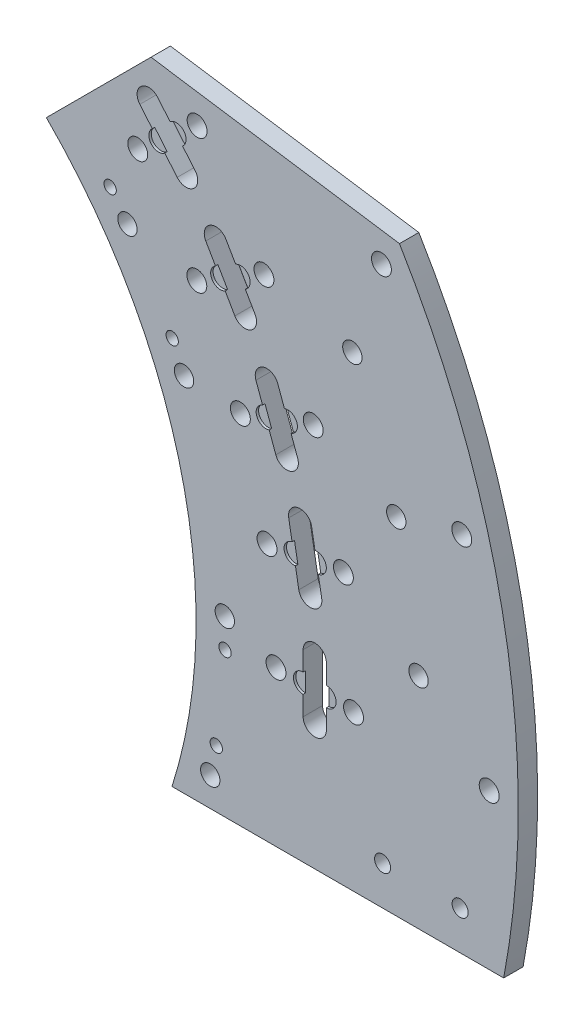
SolidWorks part; units mm, degrees
material "6061-T6 (SS)"
ref_plane "Front Plane" through (0, 0, 0) normal (0, 0, 1) x (1, 0, 0)
ref_plane "Top Plane" through (0, 0, 0) normal (0, 1, 0) x (1, 0, 0)
ref_plane "Right Plane" through (0, 0, 0) normal (1, 0, 0) x (0, 0, -1)
sketch "Sketch1" plane through (0, 0, 0) normal (0, 0, 1) x (1, 0, 0)
  line L0 (0, 0) -> (177.8, 0) construction
  line L1 (176.8984, 6.1774) -> (0, 0) construction
  line L2 (0, 0) -> (121.7947, 121.7947) construction
  line L3 (121.7947, 121.7947) -> (122.9173, 122.9173) construction
  line L4 (144.995, 101.5266) -> (0, 0) construction
  line L5 (0, 0) -> (163.5325, 67.7374) construction
  line L6 (167.4812, 0) -> (167.4812, -50.8) construction
  line L8 (159.5911, -50.8) -> (167.4812, -50.8) construction
  line L9 (172.1267, -41.275) -> (0, 0) construction
  line L10 (159.5911, -50.8) -> (268.2828, -50.8)
  line L11 (118.4271, 118.4271) -> (152.7152, 152.7152)
  line L12 (177.8, 0) -> (193.675, 0) construction
  line L13 (202.565, 0) -> (210.185, 0) construction
  line L14 (210.185, 0) -> (219.075, 0) construction
  line L15 (193.675, 0) -> (202.565, 0) construction
  line L16 (202.565, 0) -> (202.565, 9.525)
  line L17 (202.565, 0) -> (202.565, -9.525)
  line L18 (210.185, 9.525) -> (210.185, 0)
  line L19 (210.185, 0) -> (210.185, -9.525)
  line L20 (202.565, -9.525) -> (210.185, -9.525) construction
  line L21 (202.565, 9.525) -> (210.185, 9.525) construction
  line L22 (210.185, 9.525) -> (219.075, 0) construction
  line L23 (202.565, 9.525) -> (193.675, 0) construction
  line L24 (199.4876, 35.175) -> (201.1416, 25.7947)
  line L25 (199.4876, 35.175) -> (197.8336, 44.5553)
  line L26 (205.3378, 45.8785) -> (206.9918, 36.4982)
  line L27 (206.9918, 36.4982) -> (208.6458, 27.1179)
  line L28 (190.3488, 69.2813) -> (193.6066, 60.3307)
  line L29 (190.3488, 69.2813) -> (187.0911, 78.2319)
  line L30 (194.2516, 80.8381) -> (197.5093, 71.8875)
  line L31 (197.5093, 71.8875) -> (200.767, 62.9369)
  line L32 (175.4264, 101.2825) -> (180.1889, 93.0336)
  line L33 (175.4264, 101.2825) -> (170.6639, 109.5314)
  line L34 (177.263, 113.3414) -> (182.0255, 105.0925)
  line L35 (182.0255, 105.0925) -> (186.788, 96.8436)
  line L36 (155.1738, 130.2063) -> (161.2963, 122.9097)
  line L37 (155.1738, 130.2063) -> (149.0512, 137.5028)
  line L38 (154.8885, 142.4009) -> (161.0111, 135.1043)
  line L39 (161.0111, 135.1043) -> (167.1336, 127.8077)
  line L40 (0, 0) -> (193.675, 0) construction
  line L41 (0, 0) -> (190.7326, 33.6313) construction
  line L42 (0, 0) -> (254, 0) construction
  line L43 (254, 0) -> (263.525, 0) construction
  line L44 (254.5456, 68.2053) -> (0, 0) construction
  line L45 (152.7152, 152.7152) -> (234.123, 140.5088)
  line L46 (167.8212, 140.8187) -> (228.2193, 131.7625) construction
  line L47 (254.5456, 68.2053) -> (263.746, 70.6705) construction
  line L48 (0, 0) -> (240.3818, 21.0307) construction
  line L49 (0, 0) -> (240.3818, 21.0307) construction
  line L50 (0, 0) -> (233.0779, 62.453) construction
  line L51 (215.9, -50.8) -> (215.9, -25.4) construction
  line L52 (215.9, -25.4) -> (266.7, -25.4) construction
  line L53 (266.7, -25.4) -> (266.7, -50.8) construction
  line L54 (228.6, -38.1) -> (254, -38.1) construction
  line L55 (0, 0) -> (159.6519, 76.4361) construction
  line L56 (0, 0) -> (139.3238, 109.1792) construction
  arc A0 (172.2437, 0) -> (121.7947, 121.7947) centre (0, 0) ccw construction
  arc A1 (173.8312, 0) -> (122.9173, 122.9173) centre (0, 0) ccw construction
  circle A2 centre (176.8984, 6.1774) radius 3.175
  circle A3 centre (144.995, 101.5266) radius 3.175
  circle A4 centre (163.5325, 67.7374) radius 3.175
  arc A5 (167.4812, 0) -> (118.4271, 118.4271) centre (0, 0) ccw
  arc A6 (167.4812, 0) -> (159.5911, -50.8) centre (0, 0) cw
  arc A7 (173.8312, 0) -> (166.2428, -50.8) centre (0, 0) cw construction
  circle A8 centre (172.1267, -41.275) radius 3.175
  circle A9 centre (193.675, 0) radius 9.525 construction
  circle A10 centre (219.075, 0) radius 9.525 construction
  arc A11 (202.565, -9.525) -> (210.185, -9.525) centre (206.375, -9.525) ccw
  arc A12 (202.565, 9.525) -> (210.185, 9.525) centre (206.375, 9.525) cw
  circle A13 centre (193.675, 0) radius 3.2639
  circle A14 centre (219.075, 0) radius 3.2639
  circle A15 centre (215.7468, 38.042) radius 3.2639
  arc A16 (201.1416, 25.7947) -> (208.6458, 27.1179) centre (204.8937, 26.4563) ccw
  arc A17 (197.8336, 44.5553) -> (205.3378, 45.8785) centre (201.5857, 45.2169) cw
  circle A18 centre (190.7326, 33.6313) radius 3.2639
  circle A19 centre (205.8632, 74.9281) radius 3.2639
  arc A20 (193.6066, 60.3307) -> (200.767, 62.9369) centre (197.1868, 61.6338) ccw
  arc A21 (187.0911, 78.2319) -> (194.2516, 80.8381) centre (190.6713, 79.535) cw
  circle A22 centre (181.995, 66.2408) radius 3.2639
  circle A23 centre (189.7245, 109.5375) radius 3.2639
  arc A24 (180.1889, 93.0336) -> (186.788, 96.8436) centre (183.4885, 94.9386) ccw
  arc A25 (170.6639, 109.5314) -> (177.263, 113.3414) centre (173.9635, 111.4364) cw
  circle A26 centre (167.7275, 96.8375) radius 3.2639
  circle A27 centre (167.8212, 140.8187) radius 3.2639
  arc A28 (161.2963, 122.9097) -> (167.1336, 127.8077) centre (164.215, 125.3587) ccw
  arc A29 (149.0512, 137.5028) -> (154.8885, 142.4009) centre (151.9699, 139.9519) cw
  circle A30 centre (148.3637, 124.4919) radius 3.2639
  circle A31 centre (263.525, 0) radius 3.2639
  circle A32 centre (254.5456, 68.2053) radius 3.2639
  circle A33 centre (228.2193, 131.7625) radius 3.2639
  arc A34 (234.123, 140.5088) -> (268.2828, -50.8) centre (0, 0) cw
  circle A36 centre (240.3818, 21.0307) radius 3.175
  circle A37 centre (233.0779, 62.453) radius 3.175
  circle A38 centre (218.6921, 101.9778) radius 3.175
  arc A39 (210.185, 0) -> (203.9537, -50.8) centre (0, 0) cw construction
  circle A40 centre (228.6, -38.1) radius 2.6289
  circle A41 centre (254, -38.1) radius 2.6289
  circle A42 centre (159.6519, 76.4361) radius 9.525 construction
  circle A43 centre (159.6519, 76.4361) radius 2.0193
  circle A44 centre (159.6519, 76.4361) radius 3.175 construction
  circle A45 centre (139.3238, 109.1792) radius 2.0193
  circle A46 centre (139.3238, 109.1792) radius 9.525 construction
  circle A47 centre (176.9746, -3.3473) radius 2.0193
  circle A48 centre (176.9746, -3.3473) radius 9.525 construction
  circle A49 centre (174.0977, -31.9562) radius 2.0193
  circle A50 centre (174.0977, -31.9562) radius 9.525 construction
  point P3 (172.2437, 0)
  point P96 (0, 0)
  point P114 (266.7, -38.1)
  point P132 (0, 0)
  dimension "D3" = 1.5875
  dimension "D4" = 6.35
  dimension "D5" = 2
  dimension "D7" = 10
  dimension "D8" = 6.35
  dimension "D9" = 6.35
  dimension "D11" = 6.35
  dimension "D13" = 6.35
  dimension "D15" = 19.05
  dimension "D16" = 7.62
  dimension "D17" = 19.05
  dimension "D21" = 15.875
  dimension "D22" = 6.5278
  dimension "D23" = 6.5278
  dimension "D28" = 6.5278
  dimension "D32" = 9.525
  dimension "D33" = 5
  dimension "D34" = 241.3
  dimension "D35" = 6.35
  dimension "D38" = 25.4
  dimension "D40" = 5.2578
  dimension "D41" = 5.2578
  dimension "D43" = 12.7
  dimension "D45" = 263.525
  dimension "D46" = 19.05
  dimension "D47" = 4.0386
  dimension "D48" = 6.35
  dimension "D51" = 4.0386
  dimension "D52" = 19.05
  dimension "D1" = 177.8
  dimension "D2" = 5.5562
  dimension "D6" = 45
  dimension "D10" = 22.5
  dimension "D12" = 50.8
  dimension "D14" = 9.525
  dimension "D18" = 9.525
  dimension "D19" = 9.525
  dimension "D20" = 25.4
  dimension "D25" = 10
  dimension "D26" = 254
  dimension "D27" = 9.525
  dimension "D30" = 15
  dimension "D31" = 9.525
  dimension "D37" = 10
  dimension "D39" = 50.8
  dimension "D42" = 25.4
  dimension "D44" = 215.9
  dimension "D50" = 12.5
  dimension "D54" = 12.7
  dimension "D24" = 5
  dimension "D29" = 3
  dimension "D36" = 3
  dimension "D49" = 2
  dimension "D53" = 2
extrude "Boss-Extrude1" add sketch "Sketch1" along normal blind 6.35 contours A34 L45 L11 A5 A6 L10 A33 A32 A31 A30 A27 A26 A23 A22 A19 A18 A15 A14 A13 A8 A4 A3 A2 L16 A12 L18 L19 A11 L17 L25 A17 L26
sketch "Sketch2" plane through (0, 0, 6.35) normal (0, 0, 1) x (1, 0, 0)
  line L0 (202.565, -9.525) -> (202.565, 9.525) construction
  line L1 (210.185, 9.525) -> (210.185, -9.525) construction
  line L2 (0, 0) -> (202.565, 0) construction
  line L3 (0, 0) -> (199.4876, 35.175) construction
  circle A0 centre (202.565, 0) radius 3.175
  circle A1 centre (210.185, 0) radius 3.175
  circle A2 centre (199.4876, 35.175) radius 3.175
  circle A3 centre (206.9918, 36.4982) radius 3.175
  circle A4 centre (190.3488, 69.2813) radius 3.175
  circle A5 centre (197.5093, 71.8875) radius 3.175
  circle A6 centre (175.4264, 101.2825) radius 3.175
  circle A7 centre (182.0255, 105.0925) radius 3.175
  circle A8 centre (155.1738, 130.2063) radius 3.175
  circle A9 centre (161.0111, 135.1043) radius 3.175
  dimension "D1" = 6.35
  dimension "D2" = 6.35
  dimension "D4" = 10
  dimension "D3" = 5
extrude "Cut-Extrude1" cut sketch "Sketch2" against normal blind 0.7937
sketch "Sketch3" plane through (0, 0, 6.35) normal (0, 0, 1) x (1, 0, 0)
  line L0 (0, 0) -> (167.4812, 0) construction
  line L1 (159.5911, -50.8) -> (159.5911, 0) construction
  arc A0 (159.5911, -50.8) -> (118.4271, 118.4271) centre (0, 0) ccw construction
  dimension "D1" = 7.8901
